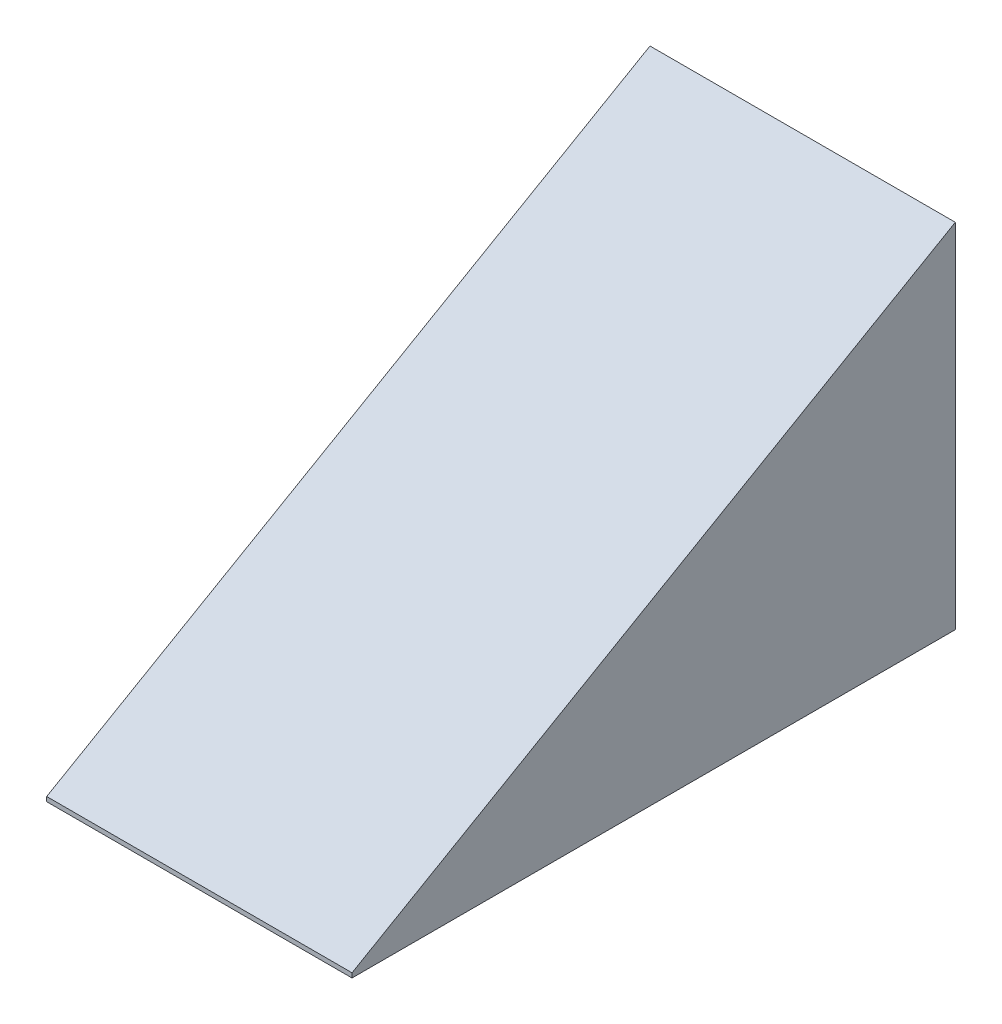
SolidWorks part; units mm, degrees
ref_plane "Front Plane"
ref_plane "Top Plane" through (0, 0, 0) normal (0, 1, 0) x (1, 0, 0)
ref_plane "Right Plane" through (0, 0, 0) normal (1, 0, 0) x (0, 0, -1)
sketch "Sketch1" plane through (0, 0, 0) normal (0, 0, 1) x (1, 0, 0)
  line L1 (-44.45, 99.06) -> (44.45, 99.06)
  line L2 (-44.45, 99.06) -> (-44.45, -53.34)
  line L3 (-44.45, -53.34) -> (44.45, -53.34)
  line L4 (44.45, 99.06) -> (44.45, -53.34)
  line L5 (-44.45, 99.06) -> (44.45, -53.34) construction
  line L6 (-44.45, -53.34) -> (44.45, 99.06) construction
  point P0 (0, 22.86)
  dimension "D1" = 88.9
  dimension "D2" = 152.4
  dimension "D3" = 22.86
extrude "Boss-Extrude1" add sketch "Sketch1" along normal blind 406.4
shell "Shell1" thickness 3.175
sketch "Sketch2" plane through (0, 0, 0) normal (1, 0, 0) x (0, 0, -1)
  line L0 (0, -56.515) -> (0, 102.235) construction
  line L2 (0, 49.53) -> (0, -49.53)
  line L3 (0, -49.53) -> (-169.3772, -49.53)
  line L4 (-169.3772, -48.26) -> (-169.3772, -49.53)
  line L5 (-169.3772, -48.26) -> (0, 49.53)
  line L6 (-169.3772, -48.26) -> (-171.577, -49.53) construction
  line L7 (-171.577, -49.53) -> (-169.3772, -49.53) construction
  point P6 (0, 0)
  dimension "D1" = 1.27
  dimension "D2" = 30
  dimension "D3" = 99.06
extrude "Boss-Extrude2" add sketch "Sketch2" along normal mid plane 85.725 separate body
delete or keep bodies "Body-Delete/Keep 1" type delete bodies bodies 101
ref_point "Point2"
sketch "Sketch3" plane through (0, 0, 0) normal (0, 0, -1) x (-1, 0, 0)
  circle A0 centre (0, 0) radius 4.4323
  dimension "D1" = 8.8646
extrude "Cut-Extrude1" [suppressed] cut sketch "Sketch3" against normal blind 10.16 draft 8
sketch "Sketch4" plane through (0, 0, 0) normal (0, 0, -1) x (-1, 0, 0)
  circle A0 centre (0, 0) radius 2.8702
  dimension "D1" = 5.7404
extrude "Cut-Extrude2" cut sketch "Sketch4" against normal blind 6.35 draft 8
